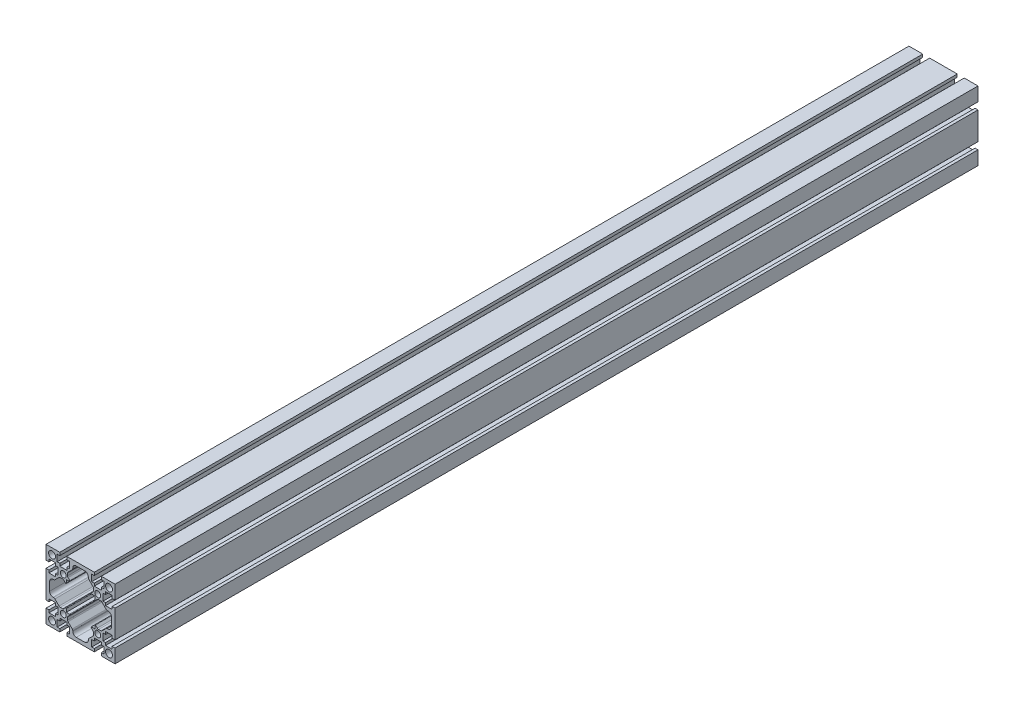
SolidWorks part; units mm, degrees
material "6063 T5"
ref_plane "Спереди" through (0, 0, 0) normal (0, 0, 1) x (1, 0, 0)
ref_plane "Сверху" through (0, 0, 0) normal (0, 1, 0) x (1, 0, 0)
ref_plane "Справа" through (0, 0, 0) normal (1, 0, 0) x (0, 0, -1)
sketch "Эскиз1" plane through (0, 0, 0) normal (0, 0, 1) x (1, 0, 0)
  line L0 (-30.8266, 161.2383) -> (49.1734, 161.2383) construction
  line L1 (0, 40) -> (0, -40) construction
  line L2 (-40, 0) -> (40, 0) construction
  line L3 (-40, 27.05) -> (-40, 40)
  line L4 (-40, 40) -> (-27.05, 40)
  line L5 (-35.8, -5) -> (-35.8, 5)
  line L6 (-31.8, 9) -> (-31.1284, 9)
  line L7 (-29.7142, 9.5858) -> (-24.8858, 14.4142)
  line L8 (-23.4716, 15) -> (-20.8284, 15)
  line L9 (-19.4142, 14.4142) -> (-17.3536, 12.3536)
  line L10 (-16.5, 12.7071) -> (-16.5, 16.5)
  line L11 (-16.5, 16.5) -> (0, 0) construction
  line L12 (-12.7071, 16.5) -> (-16.5, 16.5)
  line L13 (-14.4142, 19.4142) -> (-12.3536, 17.3536)
  line L14 (-15, 23.4716) -> (-15, 20.8284)
  line L15 (-9.5858, 29.7142) -> (-14.4142, 24.8858)
  line L16 (-9, 31.8) -> (-9, 31.1284)
  line L17 (0, 35.8) -> (-5, 35.8)
  line L18 (-40, 12.95) -> (-40, -12.95)
  line L19 (-12.95, 40) -> (0, 40)
  line L20 (0, -35.8) -> (-5, -35.8)
  line L21 (-9, -31.8) -> (-9, -31.1284)
  line L22 (-9.5858, -29.7142) -> (-14.4142, -24.8858)
  line L23 (-15, -23.4716) -> (-15, -20.8284)
  line L24 (-14.4142, -19.4142) -> (-12.3536, -17.3536)
  line L25 (-12.7071, -16.5) -> (-16.5, -16.5)
  line L26 (-16.5, -12.7071) -> (-16.5, -16.5)
  line L27 (-19.4142, -14.4142) -> (-17.3536, -12.3536)
  line L28 (-23.4716, -15) -> (-20.8284, -15)
  line L29 (-29.7142, -9.5858) -> (-24.8858, -14.4142)
  line L30 (-31.8, -9) -> (-31.1284, -9)
  line L31 (-40, -27.05) -> (-40, -40)
  line L32 (-40, -40) -> (-27.05, -40)
  line L33 (-12.95, -40) -> (0, -40)
  line L34 (40, -27.05) -> (40, -40)
  line L35 (40, -40) -> (27.05, -40)
  line L36 (35.8, 5) -> (35.8, -5)
  line L37 (31.8, -9) -> (31.1284, -9)
  line L38 (29.7142, -9.5858) -> (24.8858, -14.4142)
  line L39 (23.4716, -15) -> (20.8284, -15)
  line L40 (19.4142, -14.4142) -> (17.3536, -12.3536)
  line L41 (16.5, -12.7071) -> (16.5, -16.5)
  line L42 (12.7071, -16.5) -> (16.5, -16.5)
  line L43 (14.4142, -19.4142) -> (12.3536, -17.3536)
  line L44 (15, -23.4716) -> (15, -20.8284)
  line L45 (9.5858, -29.7142) -> (14.4142, -24.8858)
  line L46 (9, -31.8) -> (9, -31.1284)
  line L47 (0, -35.8) -> (5, -35.8)
  line L48 (40, -12.95) -> (40, 12.95)
  line L49 (12.95, -40) -> (0, -40)
  line L50 (0, 35.8) -> (5, 35.8)
  line L51 (9, 31.8) -> (9, 31.1284)
  line L52 (9.5858, 29.7142) -> (14.4142, 24.8858)
  line L53 (15, 23.4716) -> (15, 20.8284)
  line L54 (14.4142, 19.4142) -> (12.3536, 17.3536)
  line L55 (12.7071, 16.5) -> (16.5, 16.5)
  line L56 (16.5, 12.7071) -> (16.5, 16.5)
  line L57 (19.4142, 14.4142) -> (17.3536, 12.3536)
  line L58 (23.4716, 15) -> (20.8284, 15)
  line L59 (29.7142, 9.5858) -> (24.8858, 14.4142)
  line L60 (31.8, 9) -> (31.1284, 9)
  line L61 (40, 27.05) -> (40, 40)
  line L62 (40, 40) -> (27.05, 40)
  line L63 (12.95, 40) -> (0, 40)
  line L64 (16.5, -16.5) -> (0, 0) construction
  circle A0 centre (-33, 33) radius 4
  circle A1 centre (-20, 20) radius 3.4
  arc A2 (-35.8, 5) -> (-31.8, 9) centre (-31.8, 5) cw
  arc A3 (-20.8284, 15) -> (-19.4142, 14.4142) centre (-20.8284, 13) cw
  arc A4 (-24.8858, 14.4142) -> (-23.4716, 15) centre (-23.4716, 13) cw
  arc A5 (-31.1284, 9) -> (-29.7142, 9.5858) centre (-31.1284, 11) ccw
  arc A6 (-17.3536, 12.3536) -> (-16.5, 12.7071) centre (-17, 12.7071) ccw
  arc A7 (-12.3536, 17.3536) -> (-12.7071, 16.5) centre (-12.7071, 17) cw
  arc A8 (-15, 20.8284) -> (-14.4142, 19.4142) centre (-13, 20.8284) ccw
  arc A9 (-14.4142, 24.8858) -> (-15, 23.4716) centre (-13, 23.4716) ccw
  arc A10 (-9, 31.1284) -> (-9.5858, 29.7142) centre (-11, 31.1284) cw
  arc A11 (-5, 35.8) -> (-9, 31.8) centre (-5, 31.8) ccw
  arc A12 (-5, -35.8) -> (-9, -31.8) centre (-5, -31.8) cw
  arc A13 (-9, -31.1284) -> (-9.5858, -29.7142) centre (-11, -31.1284) ccw
  arc A14 (-14.4142, -24.8858) -> (-15, -23.4716) centre (-13, -23.4716) cw
  arc A15 (-15, -20.8284) -> (-14.4142, -19.4142) centre (-13, -20.8284) cw
  arc A16 (-12.3536, -17.3536) -> (-12.7071, -16.5) centre (-12.7071, -17) ccw
  arc A17 (-17.3536, -12.3536) -> (-16.5, -12.7071) centre (-17, -12.7071) cw
  arc A18 (-20.8284, -15) -> (-19.4142, -14.4142) centre (-20.8284, -13) ccw
  arc A19 (-24.8858, -14.4142) -> (-23.4716, -15) centre (-23.4716, -13) ccw
  arc A20 (-31.1284, -9) -> (-29.7142, -9.5858) centre (-31.1284, -11) cw
  arc A21 (-35.8, -5) -> (-31.8, -9) centre (-31.8, -5) ccw
  circle A22 centre (-20, -20) radius 3.4
  circle A23 centre (-33, -33) radius 4
  circle A24 centre (33, -33) radius 4
  circle A25 centre (20, -20) radius 3.4
  arc A26 (35.8, -5) -> (31.8, -9) centre (31.8, -5) cw
  arc A27 (20.8284, -15) -> (19.4142, -14.4142) centre (20.8284, -13) cw
  arc A28 (24.8858, -14.4142) -> (23.4716, -15) centre (23.4716, -13) cw
  arc A29 (31.1284, -9) -> (29.7142, -9.5858) centre (31.1284, -11) ccw
  arc A30 (17.3536, -12.3536) -> (16.5, -12.7071) centre (17, -12.7071) ccw
  arc A31 (12.3536, -17.3536) -> (12.7071, -16.5) centre (12.7071, -17) cw
  arc A32 (15, -20.8284) -> (14.4142, -19.4142) centre (13, -20.8284) ccw
  arc A33 (14.4142, -24.8858) -> (15, -23.4716) centre (13, -23.4716) ccw
  arc A34 (9, -31.1284) -> (9.5858, -29.7142) centre (11, -31.1284) cw
  arc A35 (5, -35.8) -> (9, -31.8) centre (5, -31.8) ccw
  arc A36 (5, 35.8) -> (9, 31.8) centre (5, 31.8) cw
  arc A37 (9, 31.1284) -> (9.5858, 29.7142) centre (11, 31.1284) ccw
  arc A38 (14.4142, 24.8858) -> (15, 23.4716) centre (13, 23.4716) cw
  arc A39 (15, 20.8284) -> (14.4142, 19.4142) centre (13, 20.8284) cw
  arc A40 (12.3536, 17.3536) -> (12.7071, 16.5) centre (12.7071, 17) ccw
  arc A41 (17.3536, 12.3536) -> (16.5, 12.7071) centre (17, 12.7071) cw
  arc A42 (20.8284, 15) -> (19.4142, 14.4142) centre (20.8284, 13) ccw
  arc A43 (24.8858, 14.4142) -> (23.4716, 15) centre (23.4716, 13) ccw
  arc A44 (31.1284, 9) -> (29.7142, 9.5858) centre (31.1284, 11) cw
  arc A45 (35.8, 5) -> (31.8, 9) centre (31.8, 5) ccw
  circle A46 centre (20, 20) radius 3.4
  circle A47 centre (33, 33) radius 4
  point P7 (-40, 20)
  point P8 (-20, 40)
  point P13 (-20, 26)
  point P17 (-26, 20)
  point P31 (-35.8, 9)
  point P36 (-24.3, 15)
  point P39 (-30.3, 9)
  point P42 (-16.5, 11.5)
  point P94 (-35.8, 0)
  point P182 (35.8, 0)
  point P187 (0, 0)
  line B0 (-27.05, 40) -> (-24.05, 40)
  line B1 (-24.05, 40) -> (-24.05, 36.6)
  line B2 (-24.05, 36.6) -> (-27.05, 36.6)
  line B3 (-27.05, 36.6) -> (-27.05, 29)
  line B4 (-27.05, 29) -> (-24.05, 29)
  line B5 (-24.05, 29) -> (-24.05, 26)
  line B6 (-24.05, 26) -> (-15.95, 26)
  line B7 (-15.95, 26) -> (-15.95, 29)
  line B8 (-15.95, 29) -> (-12.95, 29)
  line B9 (-12.95, 29) -> (-12.95, 36.6)
  line B10 (-12.95, 36.6) -> (-15.95, 36.6)
  line B11 (-15.95, 36.6) -> (-15.95, 40)
  line B12 (-15.95, 40) -> (-12.95, 40)
  line B13 (-12.95, 40) -> (-27.05, 40) construction
  line B14 (-40, 12.95) -> (-40, 15.95)
  line B15 (-40, 15.95) -> (-36.6, 15.95)
  line B16 (-36.6, 15.95) -> (-36.6, 12.95)
  line B17 (-36.6, 12.95) -> (-29, 12.95)
  line B18 (-29, 12.95) -> (-29, 15.95)
  line B19 (-29, 15.95) -> (-26, 15.95)
  line B20 (-26, 15.95) -> (-26, 24.05)
  line B21 (-26, 24.05) -> (-29, 24.05)
  line B22 (-29, 24.05) -> (-29, 27.05)
  line B23 (-29, 27.05) -> (-36.6, 27.05)
  line B24 (-36.6, 27.05) -> (-36.6, 24.05)
  line B25 (-36.6, 24.05) -> (-40, 24.05)
  line B26 (-40, 24.05) -> (-40, 27.05)
  line B27 (-40, 27.05) -> (-40, 12.95) construction
  line B28 (-27.05, -40) -> (-24.05, -40)
  line B29 (-24.05, -40) -> (-24.05, -36.6)
  line B30 (-24.05, -36.6) -> (-27.05, -36.6)
  line B31 (-27.05, -36.6) -> (-27.05, -29)
  line B32 (-27.05, -29) -> (-24.05, -29)
  line B33 (-24.05, -29) -> (-24.05, -26)
  line B34 (-24.05, -26) -> (-15.95, -26)
  line B35 (-15.95, -26) -> (-15.95, -29)
  line B36 (-15.95, -29) -> (-12.95, -29)
  line B37 (-12.95, -29) -> (-12.95, -36.6)
  line B38 (-12.95, -36.6) -> (-15.95, -36.6)
  line B39 (-15.95, -36.6) -> (-15.95, -40)
  line B40 (-15.95, -40) -> (-12.95, -40)
  line B41 (-12.95, -40) -> (-27.05, -40) construction
  line B42 (-40, -12.95) -> (-40, -15.95)
  line B43 (-40, -15.95) -> (-36.6, -15.95)
  line B44 (-36.6, -15.95) -> (-36.6, -12.95)
  line B45 (-36.6, -12.95) -> (-29, -12.95)
  line B46 (-29, -12.95) -> (-29, -15.95)
  line B47 (-29, -15.95) -> (-26, -15.95)
  line B48 (-26, -15.95) -> (-26, -24.05)
  line B49 (-26, -24.05) -> (-29, -24.05)
  line B50 (-29, -24.05) -> (-29, -27.05)
  line B51 (-29, -27.05) -> (-36.6, -27.05)
  line B52 (-36.6, -27.05) -> (-36.6, -24.05)
  line B53 (-36.6, -24.05) -> (-40, -24.05)
  line B54 (-40, -24.05) -> (-40, -27.05)
  line B55 (-40, -27.05) -> (-40, -12.95) construction
  line B56 (27.05, -40) -> (24.05, -40)
  line B57 (24.05, -40) -> (24.05, -36.6)
  line B58 (24.05, -36.6) -> (27.05, -36.6)
  line B59 (27.05, -36.6) -> (27.05, -29)
  line B60 (27.05, -29) -> (24.05, -29)
  line B61 (24.05, -29) -> (24.05, -26)
  line B62 (24.05, -26) -> (15.95, -26)
  line B63 (15.95, -26) -> (15.95, -29)
  line B64 (15.95, -29) -> (12.95, -29)
  line B65 (12.95, -29) -> (12.95, -36.6)
  line B66 (12.95, -36.6) -> (15.95, -36.6)
  line B67 (15.95, -36.6) -> (15.95, -40)
  line B68 (15.95, -40) -> (12.95, -40)
  line B69 (12.95, -40) -> (27.05, -40) construction
  line B70 (40, -12.95) -> (40, -15.95)
  line B71 (40, -15.95) -> (36.6, -15.95)
  line B72 (36.6, -15.95) -> (36.6, -12.95)
  line B73 (36.6, -12.95) -> (29, -12.95)
  line B74 (29, -12.95) -> (29, -15.95)
  line B75 (29, -15.95) -> (26, -15.95)
  line B76 (26, -15.95) -> (26, -24.05)
  line B77 (26, -24.05) -> (29, -24.05)
  line B78 (29, -24.05) -> (29, -27.05)
  line B79 (29, -27.05) -> (36.6, -27.05)
  line B80 (36.6, -27.05) -> (36.6, -24.05)
  line B81 (36.6, -24.05) -> (40, -24.05)
  line B82 (40, -24.05) -> (40, -27.05)
  line B83 (40, -27.05) -> (40, -12.95) construction
  line B84 (27.05, 40) -> (24.05, 40)
  line B85 (24.05, 40) -> (24.05, 36.6)
  line B86 (24.05, 36.6) -> (27.05, 36.6)
  line B87 (27.05, 36.6) -> (27.05, 29)
  line B88 (27.05, 29) -> (24.05, 29)
  line B89 (24.05, 29) -> (24.05, 26)
  line B90 (24.05, 26) -> (15.95, 26)
  line B91 (15.95, 26) -> (15.95, 29)
  line B92 (15.95, 29) -> (12.95, 29)
  line B93 (12.95, 29) -> (12.95, 36.6)
  line B94 (12.95, 36.6) -> (15.95, 36.6)
  line B95 (15.95, 36.6) -> (15.95, 40)
  line B96 (15.95, 40) -> (12.95, 40)
  line B97 (12.95, 40) -> (27.05, 40) construction
  line B98 (40, 12.95) -> (40, 15.95)
  line B99 (40, 15.95) -> (36.6, 15.95)
  line B100 (36.6, 15.95) -> (36.6, 12.95)
  line B101 (36.6, 12.95) -> (29, 12.95)
  line B102 (29, 12.95) -> (29, 15.95)
  line B103 (29, 15.95) -> (26, 15.95)
  line B104 (26, 15.95) -> (26, 24.05)
  line B105 (26, 24.05) -> (29, 24.05)
  line B106 (29, 24.05) -> (29, 27.05)
  line B107 (29, 27.05) -> (36.6, 27.05)
  line B108 (36.6, 27.05) -> (36.6, 24.05)
  line B109 (36.6, 24.05) -> (40, 24.05)
  line B110 (40, 24.05) -> (40, 27.05)
  line B111 (40, 27.05) -> (40, 12.95) construction
  dimension "D5" = 8
  dimension "D6" = 6.8
  dimension "D7" = 7
  dimension "D8" = 7
  dimension "D17" = 4
  dimension "D18" = 2
  dimension "D19" = 0.5
  dimension "D1" = 80
  dimension "D2" = 80
  dimension "D3" = 20
  dimension "D4" = 20
  dimension "D9" = 45
  dimension "D10" = 4.2
  dimension "D11" = 9
  dimension "D12" = 45
  dimension "D13" = 6
  dimension "D14" = 3.5
  dimension "D15" = 5
  dimension "D16" = 5.5
  dimension "D20" = 2
sketch_block_instance "8G(14,2U)-1"
sketch_block "8G(14,2U)" parameters "D6"=0.5, "D1"=14.1, "D2"=8.1, "D3"=2.3, "D4"=10, "D5"=4
sketch_block_instance "8G(14,2U)-4"
sketch_block_instance "8G(14,2U)-7"
sketch_block_instance "8G(14,2U)-8"
sketch_block_instance "8G(14,2U)-13"
sketch_block_instance "8G(14,2U)-14"
sketch_block_instance "8G(14,2U)-15"
sketch_block_instance "8G(14,2U)-16"
extrude "Бобышка-Вытянуть1" add sketch "Эскиз1" along normal blind 1000 contours B109 B110 L61 L62 B84 B85 B86 B87 B88 B89 B90 B91 B92 B93 B94 B95 B96 L63 L19 B12 B11 B10 B9 B8 B7 B6 B5 B4 B3 B2 B1 B0 L4 L3 B26 B25 B24 B23 B22 B21 B20 B19 B18 B17 B16 B15 B14 L18 B42 B43 B44
